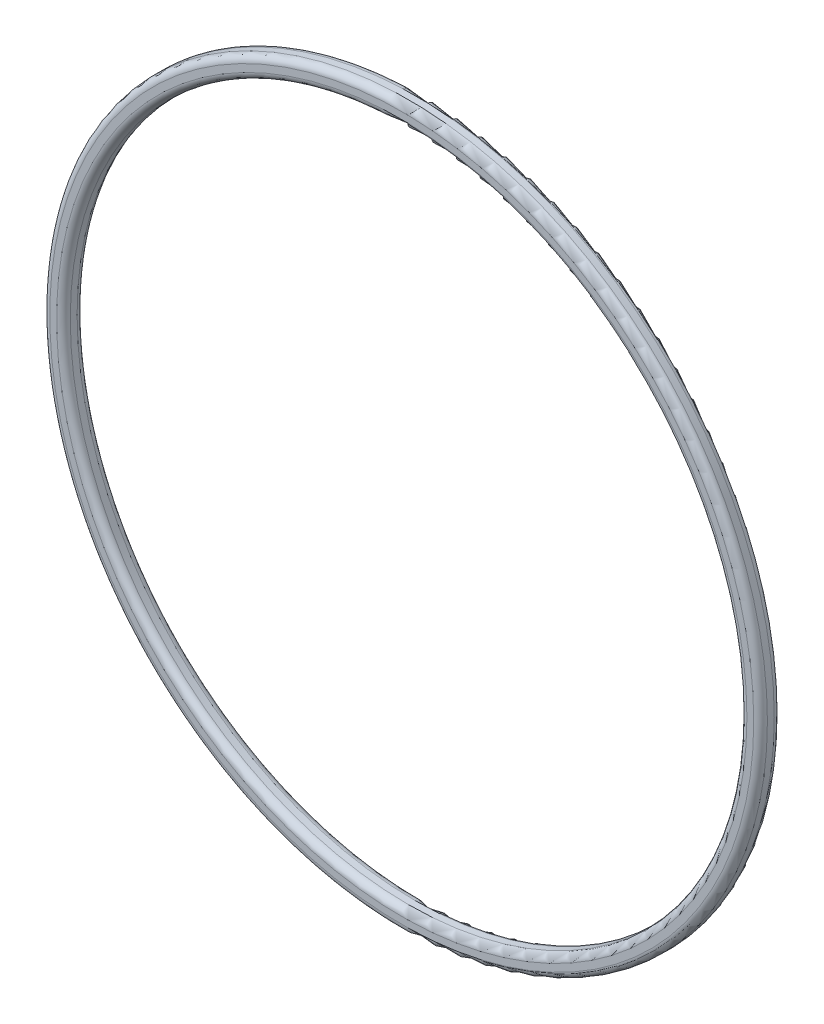
SolidWorks part; units mm, degrees
material "Gomma siliconata"
ref_plane "Piano frontale" through (0, 0, 0) normal (0, 0, 1) x (1, 0, 0)
ref_plane "Piano superiore" through (0, 0, 0) normal (0, 1, 0) x (1, 0, 0)
ref_plane "Piano destro" through (0, 0, 0) normal (1, 0, 0) x (0, 0, -1)
sketch "Schizzo1" plane through (0, 0, 0) normal (0, 0, 1) x (1, 0, 0)
  circle A0 centre (0, 0) radius 49.5
  circle A1 centre (0, 0) radius 52.5
  dimension "D1" = 99
  dimension "D2" = 105
extrude "Estrusione-Estrusione1" add sketch "Schizzo1" along normal blind 3
fillet "Raccordo1" radius 1 4 edges at (49.5, 0, 0) (52.5, 0, 0) (49.5, 0, 3) (52.5, 0, 3)
